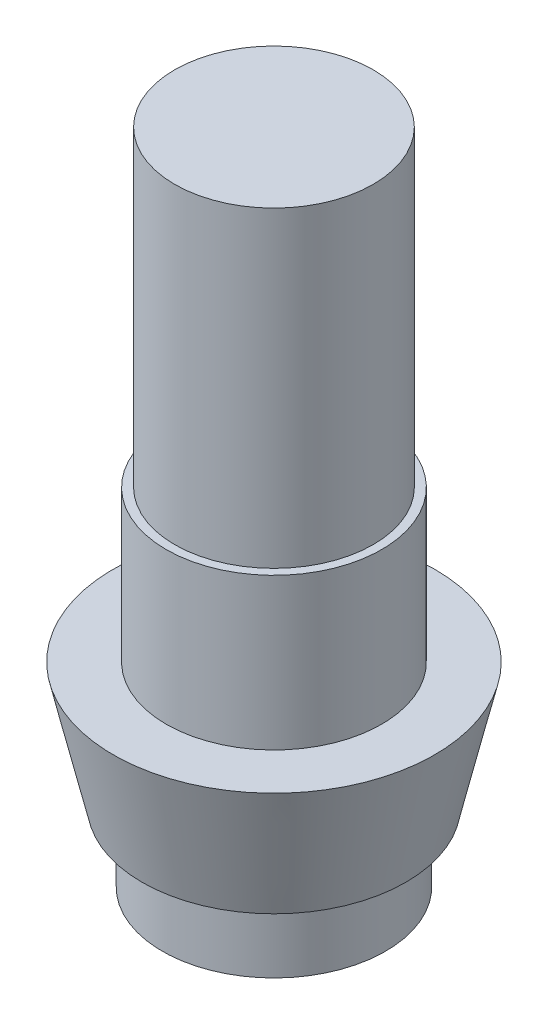
SolidWorks part; units mm, degrees
ref_plane "Спереди" through (0, 0, 0) normal (0, 0, 1) x (1, 0, 0)
ref_plane "Сверху" through (0, 0, 0) normal (0, 1, 0) x (1, 0, 0)
ref_plane "Справа" through (0, 0, 0) normal (1, 0, 0) x (0, 0, -1)
sketch "Sketch1" plane through (0, 0, 0) normal (0, 1, 0) x (1, 0, 0)
  circle A0 centre (0, 0) radius 5.7
  dimension "D1" = 11.4
extrude "Boss-Extrude1" add sketch "Sketch1" along normal blind 8
sketch "Sketch2" plane through (0, 8, 0) normal (0, 1, 0) x (1, 0, 0)
  line L0 (0, 5.7) -> (0, -5.7) construction
  circle A0 centre (0, 0) radius 5.7 construction
  circle A1 centre (0, 0) radius 5.25
  dimension "D1" = 10.5
extrude "Boss-Extrude2" add sketch "Sketch2" along normal blind 16.5
sketch "Sketch3" plane through (0, 0, 0) normal (0, -1, 0) x (1, 0, 0)
  circle A0 centre (0, 0) radius 8.5
  dimension "D1" = 17
extrude "Boss-Extrude3" add sketch "Sketch3" along normal blind 6.6 draft 13
sketch "Sketch4" plane through (0, -6.6, 0) normal (0, -1, 0) x (1, 0, 0)
  circle A0 centre (0, 0) radius 5.9
  dimension "D1" = 11.8
extrude "Boss-Extrude4" add sketch "Sketch4" along normal blind 3.7
